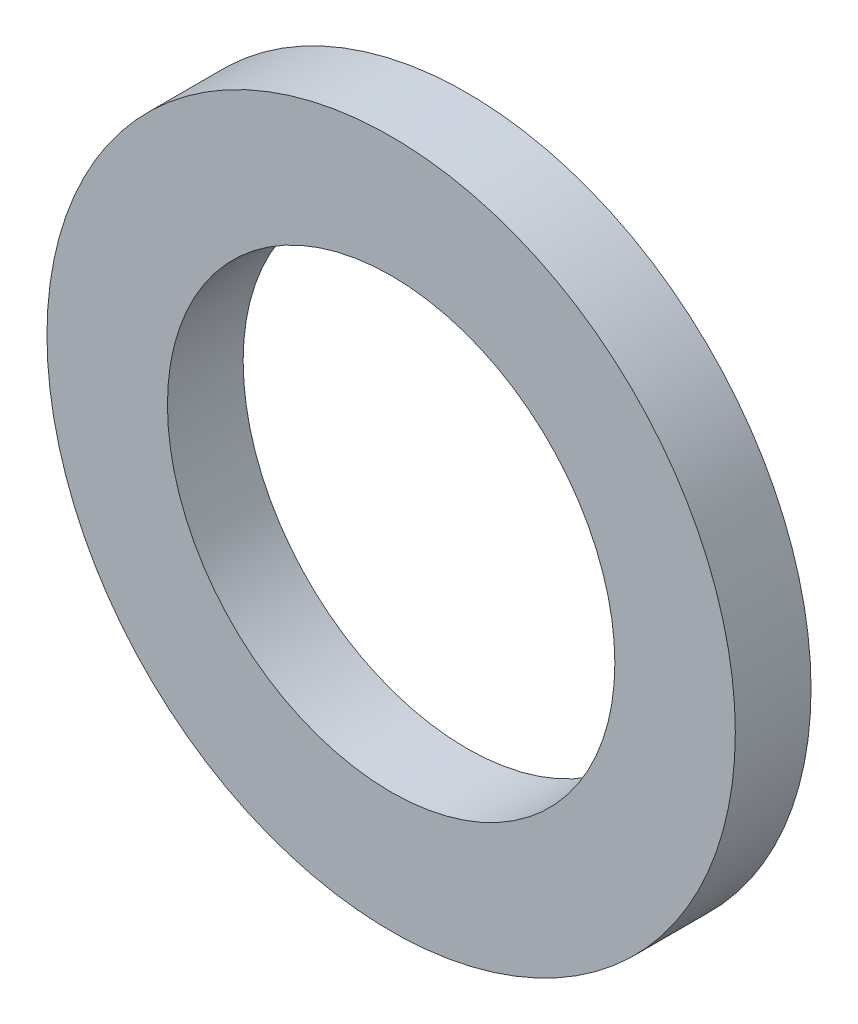
SolidWorks part; units mm, degrees
ref_plane "Ebene vorne" through (0, 0, 0) normal (0, 0, 1) x (1, 0, 0)
ref_plane "Ebene oben" through (0, 0, 0) normal (0, 1, 0) x (1, 0, 0)
ref_plane "Ebene rechts" through (0, 0, 0) normal (1, 0, 0) x (0, 0, -1)
sketch "Skizze1" plane through (0, 0, 0) normal (0, 0, 1) x (1, 0, 0)
  circle A0 centre (0, 0) radius 6.5
  circle A1 centre (0, 0) radius 10
  dimension "D1" = 13
  dimension "D2" = 20
extrude "Aufsatz-Linear austragen1" add sketch "Skizze1" along normal blind 2.2
